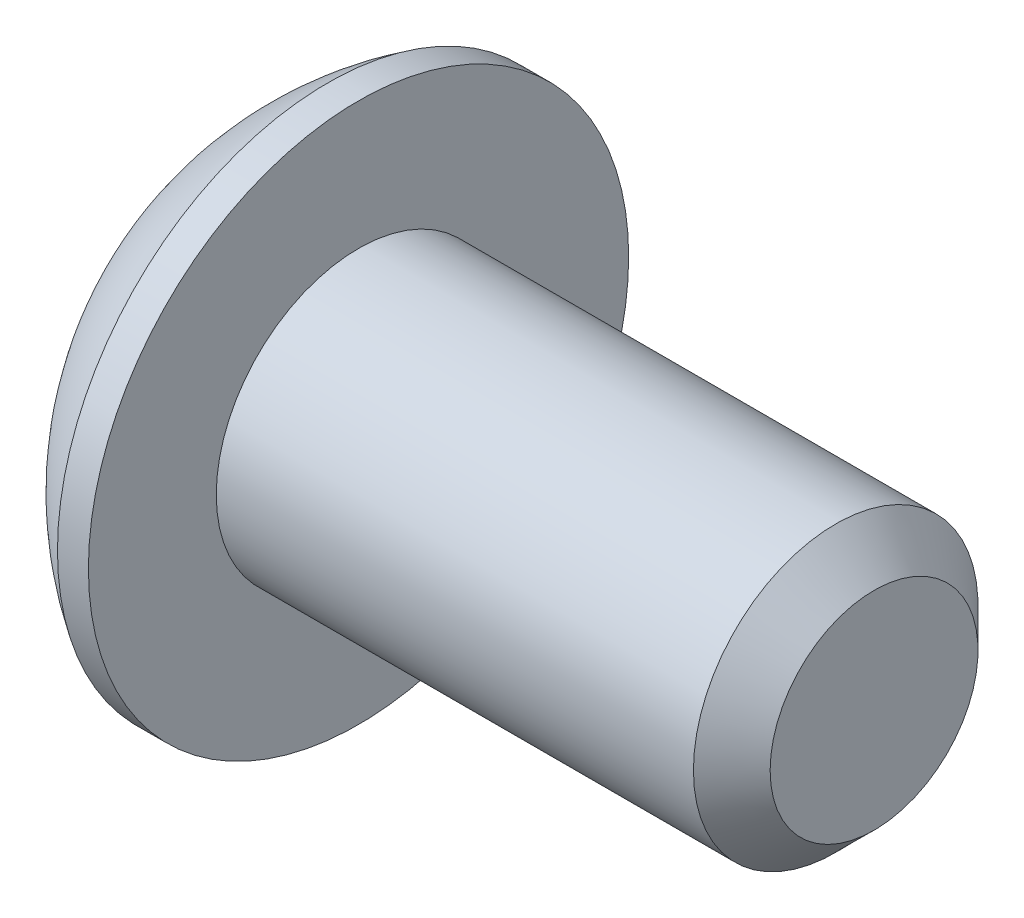
SolidWorks part; units mm, degrees
material "Plain Carbon Steel"
ref_plane "Plane1" through (0, 0, 0) normal (0, 0, 1) x (1, 0, 0)
ref_plane "Plane2" through (0, 0, 0) normal (0, 1, 0) x (1, 0, 0)
ref_plane "Plane3" through (0, 0, 0) normal (1, 0, 0) x (0, 0, -1)
sketch "BodySke" plane through (0, 0, 0) normal (0, 0, 1) x (1, 0, 0)
  line L0 (8.2042, 0) -> (8.2042, 1.2802)
  line L1 (7.7318, 1.7526) -> (1.8542, 1.7526)
  line L2 (1.8542, 1.7526) -> (1.8542, 3.3274)
  line L3 (1.8542, 3.3274) -> (1.4732, 3.3274)
  line L4 (0, 0) -> (101.6, 0) construction
  line L5 (1.8542, -3.3274) -> (1.4732, -3.3274) construction
  line L6 (55.6768, -1.7526) -> (1.8542, -1.7526) construction
  line L7 (8.2042, 0) -> (0, 0)
  line L8 (0, 1.6637) -> (0, -1.6637) construction
  line L9 (0, 0) -> (0, 1.6637)
  line L10 (8.2042, 1.2802) -> (7.7318, 1.7526)
  line L11 (8.2042, -1.2802) -> (7.7318, -1.7526) construction
  line L12 (1.8542, 9.525) -> (1.8542, -1.7526) construction
  line L13 (1.8542, 9.525) -> (1.8542, -1.7526) construction
  arc A1 (0, 1.6637) -> (1.4732, 3.3274) centre (3.5549, 0) cw
  dimension "Diameter" = 3.5052
  dimension "Length" = 6.35
  dimension "Head_dia" = 6.6548
  dimension "D1" = 3.3274
  dimension "Head_ht" = 1.8542
  dimension "Head_side_ht" = 0.381
  dimension "Minor_dia" = 2.5603
  dimension "Body_ch_ang" = 45
  dimension "Advance" = 0
  dimension "Thread_nom" = 6.35
revolve "BaseBody" add sketch "BodySke" angle 360 about L4
cosmetic thread "ThreadCosmetic" parameters "Thread_length"=6.35, "Thread_minor"=2.5603
sketch "Sketch2" plane through (0, 0, 0) normal (0, 0, 1) x (1, 0, 0)
  line L0 (0, 0.9906) -> (1.1176, 0.9906)
  line L1 (1.1176, 0.9906) -> (1.6895, 0)
  line L3 (1.6895, 0) -> (0, 0)
  line L4 (0, 0) -> (0, 0.9906)
  line L5 (0, -0.9906) -> (1.1176, -0.9906) construction
  line L6 (0, 0) -> (47.625, 0) construction
  dimension "D2" = 60
  dimension "PreBroach_depth" = 1.1176
  dimension "PreBroach_dia" = 1.9812
revolve "PreBroach" cut sketch "Sketch2" angle 360 about L6
sketch "Sketch3" plane through (0, 0, 0) normal (1, 0, 0) x (0, 0, -1)
  line L0 (-0.9906, -0.5719) -> (-0.9906, 0.5719)
  line L1 (-0.9906, 0.5719) -> (0, 1.1438)
  line L2 (0, 1.1438) -> (0.9906, 0.5719)
  line L3 (0.9906, 0.5719) -> (0.9906, -0.5719)
  line L4 (0.9906, -0.5719) -> (0, -1.1438)
  line L5 (0, -1.1438) -> (-0.9906, -0.5719)
  dimension "Hex_size" = 1.9812
  dimension "D3" = 1.9812
  dimension "D1" = 0.9906
  dimension "D2" = 0.9906
extrude "Hex" cut sketch "Sketch3" along normal blind 1.1176
equation "\"D1@BodySke\" = \"Head_dia@BodySke\" * .5"
equation "\"Thread_minor@ThreadCosmetic\"=\"Minor_dia@BodySke\""
equation "\"D1@Sketch3\" = \"Hex_size@Sketch3\" / 2"
equation "\"D2@Sketch3\" = \"D1@Sketch3\""
equation "\"D3@Sketch3\" = \"Hex_size@Sketch3\""
equation "\"Thread_length@ThreadCosmetic\" = \"Length@BodySke\""
